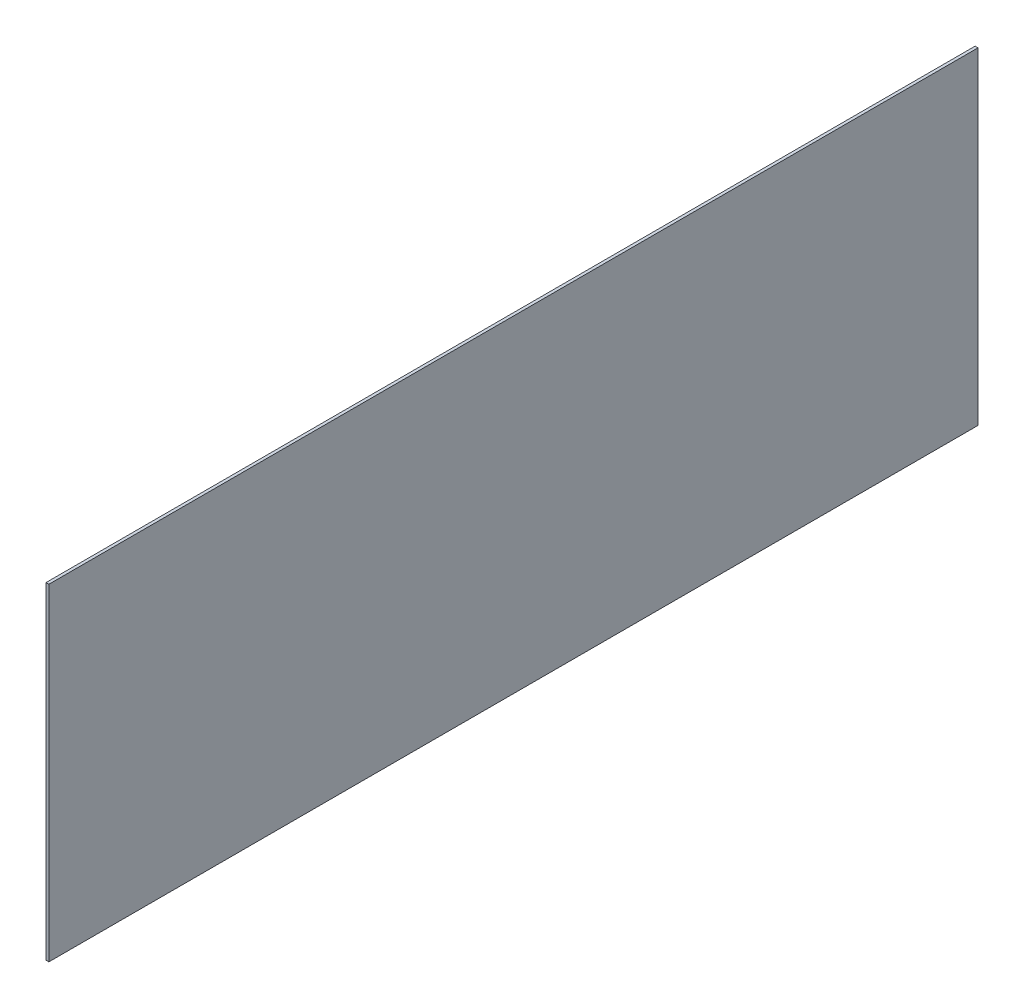
SolidWorks part; units mm, degrees
material "6061-T6 (SS)"
ref_plane "Front Plane" through (0, 0, 0) normal (0, 0, 1) x (1, 0, 0)
ref_plane "Top Plane" through (0, 0, 0) normal (0, 1, 0) x (1, 0, 0)
ref_plane "Right Plane" through (0, 0, 0) normal (1, 0, 0) x (0, 0, -1)
sketch "Sketch1" plane through (0, 0, 0) normal (1, 0, 0) x (0, 0, -1)
  line L1 (-254, -89.408) -> (254, -89.408)
  line L2 (-254, -89.408) -> (-254, 89.408)
  line L3 (-254, 89.408) -> (254, 89.408)
  line L4 (254, -89.408) -> (254, 89.408)
  line L5 (-254, -89.408) -> (254, 89.408) construction
  line L6 (-254, 89.408) -> (254, -89.408) construction
  point P0 (0, 0)
  dimension "D1" = 178.816
  dimension "D2" = 508
extrude "Boss-Extrude1" add sketch "Sketch1" along normal blind 1.5875
